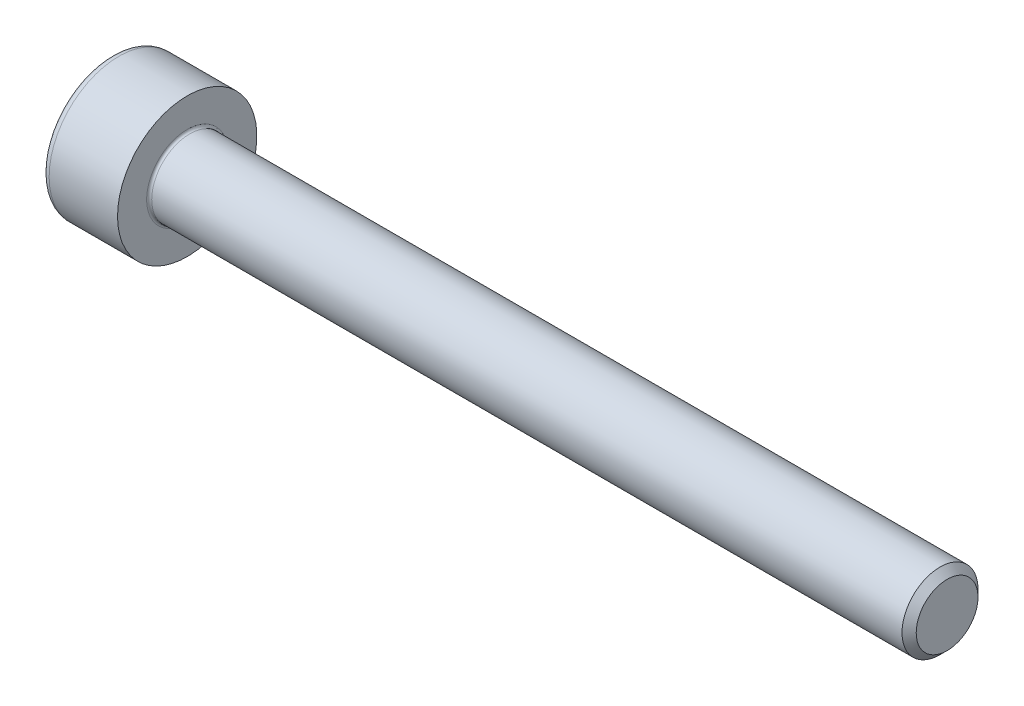
SolidWorks part; units mm, degrees
revolve "Base-Revolve" add sketch "BodySke"
sketch "BodySke" plane through (0, 0, 0) normal (0, 0, 1) x (1, 0, 0)
  line L0 (0, 0) -> (0, 2.75)
  line L1 (0, 2.75) -> (3, 2.75)
  line L2 (3, 2.75) -> (3, 1.5)
  line L3 (3, 1.5) -> (32.7195, 1.5)
  line L4 (33, 1.2195) -> (33, 0)
  line L5 (33, 0) -> (0, 0)
  line L6 (-31.75, 0) -> (127, 0) construction
  line L8 (33, 1.2195) -> (32.7195, 1.5)
  line L10 (33, -1.2195) -> (32.7195, -1.5) construction
  line L11 (3.5, 9.525) -> (3.5, 3.175) construction
  line L12 (28, 9.525) -> (28, 3.175) construction
  line L13 (-27, 9.525) -> (-27, 3.175) construction
  dimension "Head_ht" = 3
  dimension "Length" = 30
  dimension "Body_ch_ang" = 45
  dimension "Diameter" = 3
  dimension "Minor_dia" = 2.439
  dimension "Advance" = 0.5
  dimension "Thread_nom" = 5
  dimension "Thread_length" = 60
  dimension "Head_dia" = 5.5
cosmetic thread "ThreadCosmetic" [suppressed]
fillet "Fillet1" radius 0.1 1 edges at (3, 0, 1.5)
fillet "Fillet2" radius 0.3 1 edges at (0, 0, 2.75)
ref_plane "Plane1" through (0, 0, 0) normal (0, 0, 1) x (1, 0, 0)
ref_plane "Plane2" through (0, 0, 0) normal (0, 1, 0) x (1, 0, 0)
ref_plane "Plane3" through (0, 0, 0) normal (1, 0, 0) x (0, 0, -1)
other "Configuration Table"
sketch "Sketch2" plane through (0, 0, 0) normal (0, 0, 1) x (1, 0, 0)
  line L0 (0, 1.26) -> (1.3, 1.26)
  line L1 (1.3, 1.26) -> (2.0275, 0)
  line L2 (-31.75, 0) -> (127, 0) construction
  line L3 (2.0275, 0) -> (0, 0)
  line L4 (0, 0) -> (0, 1.26)
  line L6 (0, 0) -> (47.625, 0) construction
  dimension "D1" = 1.26
  dimension "D2" = 60
  dimension "Depth" = 1.3
revolve "Hex-PreBroach" cut sketch "Sketch2" angle 360 about L6
sketch "Sketch3" plane through (0, 0, 0) normal (-1, 0, 0) x (0, 0.5, 0.866)
  line L0 (0.7275, 1.26) -> (-0.7275, 1.26)
  line L1 (-0.7275, 1.26) -> (-1.4549, 0)
  line L2 (0.7275, 1.26) -> (1.4549, 0)
  line L3 (0.7275, -1.26) -> (1.4549, 0)
  line L4 (0.7275, -1.26) -> (-0.7275, -1.26)
  line L5 (-0.7275, -1.26) -> (-1.4549, 0)
  dimension "D1" = 1.26
  dimension "D2" = 1.26
  dimension "Hex_size" = 2.52
extrude "Hex" cut sketch "Sketch3" against normal blind 1.3
sketch "ThdSchSke" plane through (0, 0, 0) normal (0, 0, 1) x (1, 0, 0)
  line L0 (28, -1.2195) -> (27.8036, -1.5)
  line L1 (28, -1.2195) -> (28.1964, -1.5)
  line L2 (28.1964, -1.5) -> (28.1964, -1.875)
  line L3 (-3.175, 0) -> (5.1513, 0) construction
  line L4 (0, 2.45) -> (0, -2.45) construction
  line L5 (28.1964, -1.875) -> (27.8036, -1.875)
  line L6 (27.8036, -1.875) -> (27.8036, -1.5)
  dimension "Thread_minor" = 2.439
  dimension "Diameter" = 3
  dimension "Start" = 28
revolve "ThreadSchematic" [suppressed] cut sketch "ThdSchSke" angle 360 about L3
pattern_linear "ThdSchPat" [suppressed]
equation "\"D2@Sketch3\" = \"Hex_size@Sketch3\" / 2"
equation "\"D1@Sketch3\" = \"Hex_size@Sketch3\" / 2"
equation "\"D1@Sketch2\" = \"Hex_size@Sketch3\" / 2"
equation "\"Thread_minor@ThreadCosmetic\"  =  \"Minor_dia@BodySke\""
equation "\"Depth@Sketch2\" =  \"Key_eng@Hex\""
equation "\"Thread_length@ThreadCosmetic\" = ((sgn( (\"Length@BodySke\" - \"Advance@BodySke\" * 3.0) - \"Thread_nom@BodySke\" )-1)*( (\"Length@BodySke\" - \"Advance@BodySke\" * 3.0) - \"Thread_nom@BodySke\" ))/-2+ \"Thread_nom@BodySke\""
equation "\"Thread_minor@ThdSchSke\" = \"Minor_dia@BodySke\""
equation "\"Diameter@ThdSchSke\" = \"Diameter@BodySke\""
equation "\"Overcut@ThdSchSke\" = \"Diameter@BodySke\" * 1.25"
equation "\"Start@ThdSchSke\" = \"Head_ht@BodySke\" + \"Length@BodySke\" - \"Thread_length@ThreadCosmetic\"  '---Non-countersunk---"
equation "\"Num_threads@ThdSchPat\" = int( \"Thread_length@ThreadCosmetic\" / \"Advance@BodySke\" + 0.999 )  + 1"
equation "\"Advance@ThdSchPat\" = \"Thread_length@ThreadCosmetic\" /  (\"Num_threads@ThdSchPat\" - 1) 'relax it"
equation "\"Num_threads@ThdSchPat\" = \"Num_threads@ThdSchPat\" - sgn( \"Num_threads@ThdSchPat\" - 1) '---chamfered tips only---"
